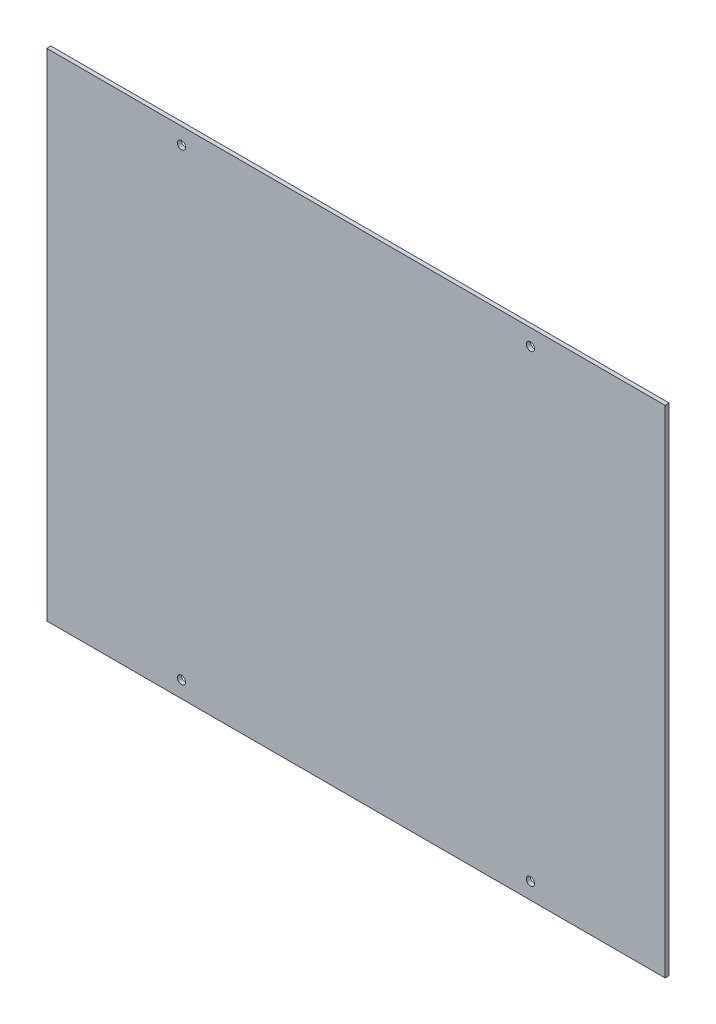
SolidWorks part; units mm, degrees
ref_plane "Front Plane" through (0, 0, 0) normal (0, 0, 1) x (1, 0, 0)
ref_plane "Top Plane" through (0, 0, 0) normal (0, 1, 0) x (1, 0, 0)
ref_plane "Right Plane" through (0, 0, 0) normal (1, 0, 0) x (0, 0, -1)
sketch "Sketch1" plane through (0, 0, 0) normal (0, 0, 1) x (1, 0, 0)
  line L0 (0, 0) -> (-206.9982, 0) construction
  line L1 (151.5, -121.5) -> (-151.5, -121.5)
  line L2 (151.5, -121.5) -> (151.5, 121.5)
  line L3 (151.5, 121.5) -> (-151.5, 121.5)
  line L4 (-151.5, -121.5) -> (-151.5, 121.5)
  line L5 (151.5, -121.5) -> (-151.5, 121.5) construction
  line L6 (151.5, 121.5) -> (-151.5, -121.5) construction
  line L7 (141.5, -113.4802) -> (-141.5, -113.4802) construction
  line L8 (141.5, -113.4802) -> (141.5, 113.4802) construction
  line L9 (141.5, 113.4802) -> (-141.5, 113.4802) construction
  line L10 (-141.5, -113.4802) -> (-141.5, 113.4802) construction
  line L11 (141.5, -113.4802) -> (-141.5, 113.4802) construction
  line L12 (141.5, 113.4802) -> (-141.5, -113.4802) construction
  circle A0 centre (-85.5, 113.4802) radius 2
  circle A1 centre (85.5, 113.4802) radius 2
  circle A2 centre (85.5, -113.4802) radius 2
  circle A3 centre (-85.5, -113.4802) radius 2
  point P0 (0, 0)
  point P5 (0, 0)
  dimension "D4" = 4
  dimension "D5" = 4
  dimension "D1" = 303
  dimension "D2" = 243
  dimension "D3" = 10
  dimension "D6" = 66
  dimension "D7" = 66
extrude "Boss-Extrude1" add sketch "Sketch1" along normal blind 2
